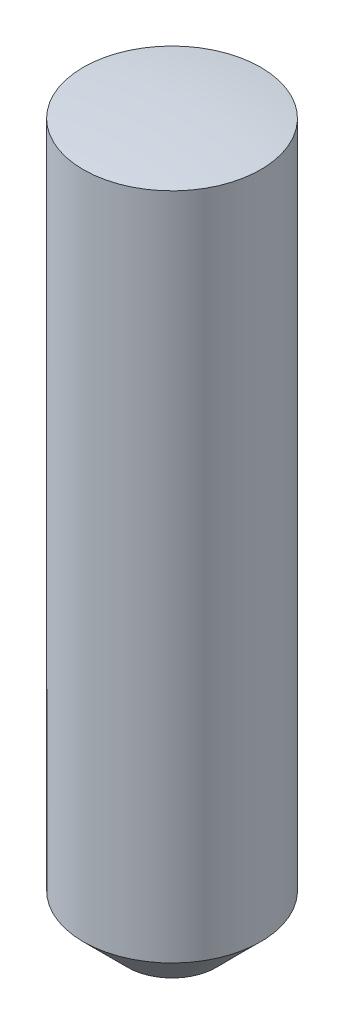
SolidWorks part; units mm, degrees
ref_plane "Front Plane" through (0, 0, 0) normal (0, 0, 1) x (1, 0, 0)
ref_plane "Top Plane" through (0, 0, 0) normal (0, 1, 0) x (1, 0, 0)
ref_plane "Right Plane" through (0, 0, 0) normal (1, 0, 0) x (0, 0, -1)
sketch "Sketch1" plane through (0, 0, 0) normal (0, 1, 0) x (1, 0, 0)
  circle A0 centre (0, 0) radius 1
  dimension "D1" = 2
extrude "Boss-Extrude 8.10mm" add sketch "Sketch1" against normal blind 8.1
chamfer "0.5 x 45 deg" distance 0.5 angle 45 1 edges at (0, -8.1, 1)
sketch "Sketch2" plane through (0, 0, 0) normal (0, 0, 1) x (1, 0, 0)
  line L0 (0, 0) -> (0, 2) construction
  line L1 (0, 2) -> (-2, 2)
  line L2 (-2, 2) -> (-2, -0.254)
  line L3 (0, 0) -> (0, 2)
  arc A0 (0, 0) -> (-2, -0.254) centre (0, -8) ccw
  dimension "D3" = 8
  dimension "D1" = 2
  dimension "D2" = 2
revolve "SR8" cut sketch "Sketch2" angle 360 about L0
